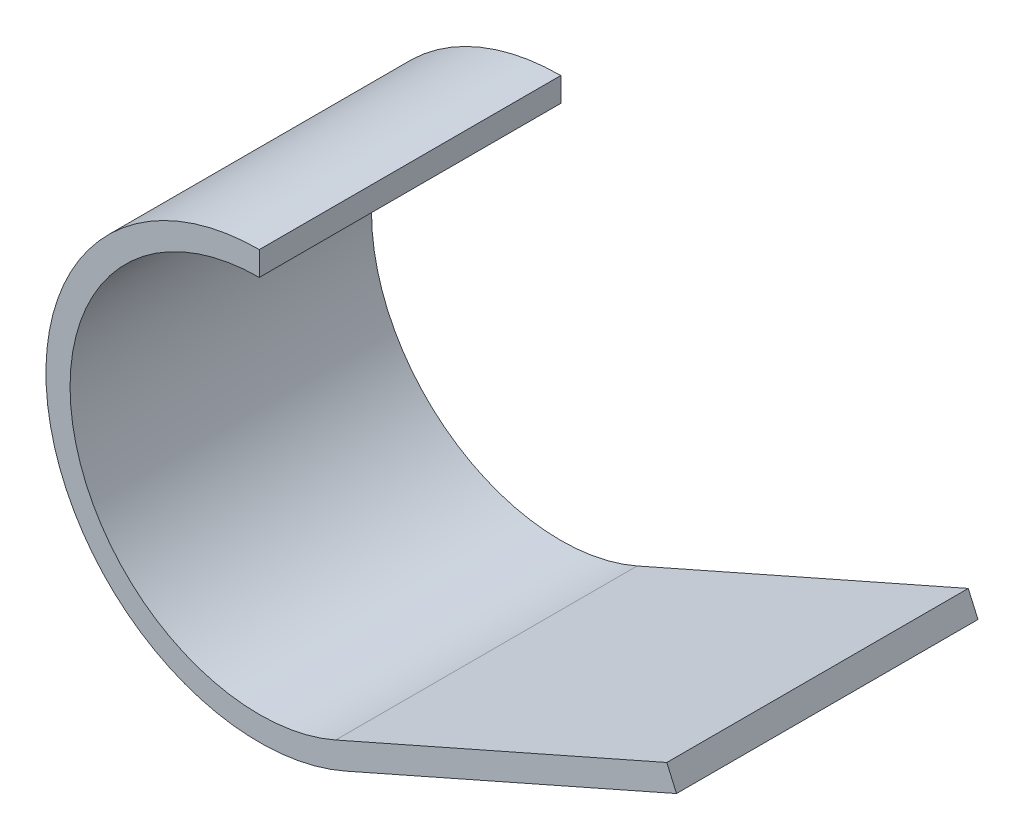
SolidWorks part; units mm, degrees
ref_plane "Front Plane" through (0, 0, 0) normal (0, 0, 1) x (1, 0, 0)
ref_plane "Top Plane" through (0, 0, 0) normal (0, 1, 0) x (1, 0, 0)
ref_plane "Right Plane" through (0, 0, 0) normal (1, 0, 0) x (0, 0, -1)
sketch "Sketch1" plane through (0, 0, 0) normal (0, 0, 1) x (1, 0, 0)
  line L0 (24.7418, -2.2452) -> (-2.7119, -14.3587)
  arc A0 (-9.0475, 15.6944) -> (-2.7119, -14.3587) centre (-9.0475, 0) ccw
extrude "Extrude-Thin1" add sketch "Sketch1" along normal blind 25 thin thin type one direction wall 2
